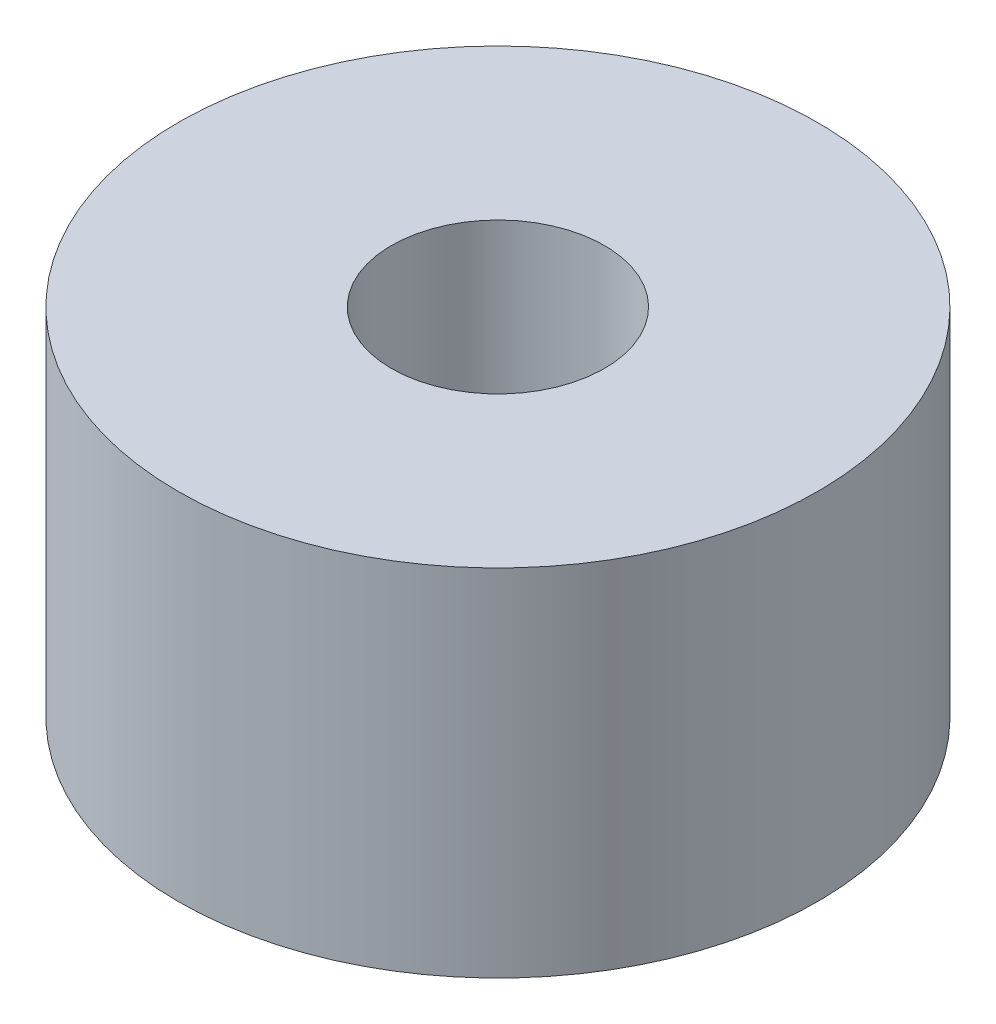
SolidWorks part; units mm, degrees
ref_plane "Front Plane" through (0, 0, 0) normal (0, 0, 1) x (1, 0, 0)
ref_plane "Top Plane" through (0, 0, 0) normal (0, 1, 0) x (1, 0, 0)
ref_plane "Right Plane" through (0, 0, 0) normal (1, 0, 0) x (0, 0, -1)
sketch "Sketch1" plane through (0, 0, 0) normal (0, 1, 0) x (1, 0, 0)
  circle A0 centre (0, 0) radius 1.5
  circle A1 centre (0, 0) radius 4.5
  dimension "D1" = 3
  dimension "D2" = 9
extrude "Boss-Extrude1" add sketch "Sketch1" along normal blind 5
